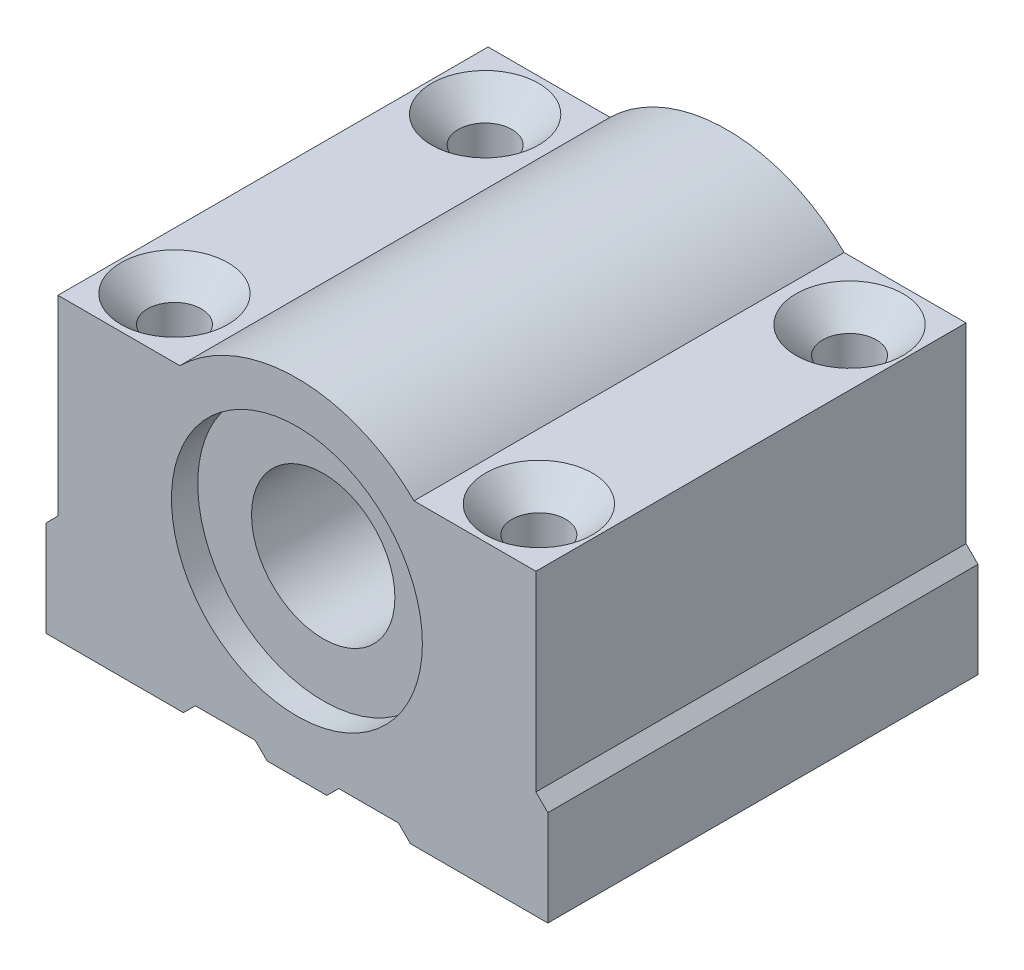
SolidWorks part; units mm, degrees
material "Liga 6061"
ref_plane "Plano frontal" through (0, 0, 0) normal (0, 0, 1) x (1, 0, 0)
ref_plane "Plano superior" through (0, 0, 0) normal (0, 1, 0) x (1, 0, 0)
ref_plane "Plano direito" through (0, 0, 0) normal (1, 0, 0) x (0, 0, -1)
sketch "Esboço1" plane through (0, 0, 0) normal (0, 0, 1) x (1, 0, 0)
  line L0 (-20, 10) -> (-20, -6)
  line L1 (-20, -6) -> (-21, -7)
  line L2 (-21, -7) -> (-21, -15)
  line L3 (-21, -15) -> (-9.5, -15)
  line L4 (-9.5, -15) -> (-8.5, -14)
  line L5 (-8.5, -14) -> (-3.5, -14)
  line L6 (8.5, -14) -> (9.5, -15)
  line L7 (9.5, -15) -> (21, -15)
  line L8 (21, -15) -> (21, -7)
  line L9 (21, -7) -> (20, -6)
  line L10 (20, -6) -> (20, 10)
  line L11 (20, 10) -> (9.798, 10)
  line L12 (-3.5, -14) -> (-2.5, -15)
  line L13 (-2.5, -15) -> (2.5, -15)
  line L14 (2.5, -15) -> (3.5, -14)
  line L15 (-9.798, 10) -> (-20, 10)
  line L16 (3.5, -14) -> (8.5, -14)
  circle A0 centre (0, 0) radius 6
  arc A1 (-9.798, 10) -> (9.798, 10) centre (0, 0) cw
  dimension "D1" = 12
  dimension "D12" = 15
  dimension "D14" = 20
  dimension "D10" = 14
  dimension "D2" = 42
  dimension "D4" = 11.5
  dimension "D5" = 1
  dimension "D8" = 25
  dimension "D9" = 8
  dimension "D11" = 40
  dimension "D13" = 21
  dimension "D15" = 15
extrude "Extrusão1" add sketch "Esboço1" along normal blind 36
sketch "Esboço2" plane through (0, 0, 36) normal (0, 0, 1) x (1, 0, 0)
  circle A0 centre (0, 0) radius 10.5
  dimension "D1" = 21
extrude "Extrusão2" cut sketch "Esboço2" against normal blind 2.2
sketch "Esboço3" plane through (0, 0, 0) normal (0, 0, -1) x (-1, 0, 0)
  circle A0 centre (0, 0) radius 10.5
  dimension "D1" = 21
extrude "Extrusão3" cut sketch "Esboço3" against normal blind 2.2
sketch "Esboço4" plane through (0, 10, 0) normal (0, 1, 0) x (1, 0, 0)
  line L3 (-21, -36) -> (-21, 0) construction
  line L4 (21, -36) -> (21, 0) construction
  line L5 (20, 0) -> (9.798, 0) construction
  circle A0 centre (15.25, -5) radius 1.65
  circle A1 centre (15.25, -31) radius 1.65
  circle A2 centre (-15.25, -5) radius 1.65
  circle A3 centre (-15.25, -31) radius 1.65
  dimension "D5" = 3.3
  dimension "D1" = 5.75
  dimension "D2" = 5.75
  dimension "D3" = 26
  dimension "D4" = 5
extrude "Extrusão4" cut sketch "Esboço4" against normal through all
hole_wizard "Escareado para parafuso de máquina com cabeça chata de M52" positions "3DSketch1" profile "Esboço6" countersink size "M5" standard "Métrico Ansi"
sketch3d "3DSketch1"
  line L0 (-15.25, -15, 31) -> (-15.25, 10, 31) construction
  line L1 (-15.25, -15, 5) -> (-15.25, 10, 5) construction
  line L2 (15.25, -15, 5) -> (15.25, 10, 5) construction
  line L3 (15.25, -15, 31) -> (15.25, 10, 31) construction
  point P0 (-15.25, -15, 31)
  point P4 (-15.25, -15, 5)
  point P8 (15.25, -15, 5)
  point P12 (15.25, -15, 31)
sketch "Esboço6" plane through (-15.25, -15, 31) normal (1, 0, 0) x (0, 0, -1)
  line L0 (0, 0) -> (0, 13.6524)
  line L1 (0, 13.6524) -> (2.75, 12)
  line L2 (2.75, 12) -> (2.75, 1.75)
  line L3 (2.75, 1.75) -> (4.5, 0)
  line L5 (4.5, 0) -> (0, 0)
  line L6 (-2.75, 1.75) -> (-4.5, 0) construction
  line L10 (0, 13.6524) -> (-2.75, 12) construction
  line L11 (0, -6.35) -> (0, 107.95) construction
  dimension "Hole Dia." = 5.5
  dimension "Hole Depth" = 12
  dimension "Near C'Sink Dia." = 9
  dimension "Near C'Sink Angle" = 90
  dimension "Drill Angle" = 118
hole_wizard "Escareado para SFHCS M41" positions "3DSketch2" profile "Esboço7" countersink size "M4" standard "Métrico Ansi" end condition through all
sketch3d "3DSketch2"
  line L0 (-15.25, -2.3391, 5) -> (-15.25, 10, 5) construction
  line L1 (-15.25, -2.3391, 31) -> (-15.25, 10, 31) construction
  line L2 (15.25, -2.3391, 31) -> (15.25, 10, 31) construction
  line L3 (15.25, -2.3391, 5) -> (15.25, 10, 5) construction
  point P0 (-15.25, 10, 5)
  point P4 (-15.25, 10, 31)
  point P8 (15.25, 10, 31)
  point P12 (15.25, 10, 5)
sketch "Esboço7" plane through (-15.25, 10, 5) normal (1, 0, 0) x (0, 0, 1)
  line L0 (0, 0) -> (0, 25)
  line L1 (0, 25) -> (2.25, 25)
  line L2 (2.25, 25) -> (2.25, 2.23)
  line L3 (2.25, 2.23) -> (4.48, 0)
  line L5 (4.48, 0) -> (0, 0)
  line L6 (-2.25, 2.23) -> (-4.48, 0) construction
  line L11 (0, -6.35) -> (0, 107.95) construction
  dimension "Thru Hole Dia." = 4.5
  dimension "Thru Hole Depth" = 25
  dimension "Near C'Sink Dia." = 8.96
  dimension "Near C'Sink Angle" = 90
